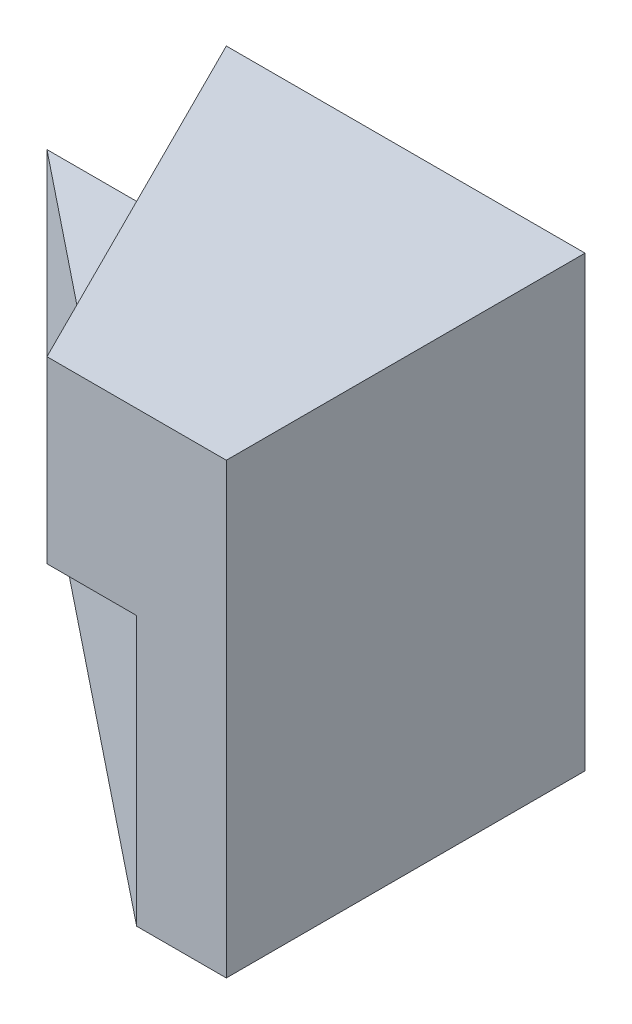
SolidWorks part; units mm, degrees
ref_plane "Front Plane" through (0, 0, 0) normal (0, 0, 1) x (1, 0, 0)
ref_plane "Top Plane" through (0, 0, 0) normal (0, 1, 0) x (1, 0, 0)
ref_plane "Right Plane" through (0, 0, 0) normal (1, 0, 0) x (0, 0, -1)
sketch "Sketch1" plane through (0, 0, 0) normal (0, 1, 0) x (1, 0, 0)
  line L0 (0, 0) -> (-5, 4)
  line L1 (-5, 4) -> (0, 4)
  line L2 (0, 4) -> (0, 0)
  dimension "D1" = 4
  dimension "D2" = 5
extrude "Boss-Extrude1" add sketch "Sketch1" along normal blind 3
sketch "Sketch2" plane through (0, 0, -4) normal (0, 0, -1) x (-1, 0, 0)
  line L0 (1, 5) -> (3, 5)
  line L1 (-1, 0) -> (-1, 5)
  line L2 (-1, 5) -> (1, 5)
  line L3 (-1, 0) -> (0, 0)
  line L4 (0, 3) -> (5, 3) construction
  line L5 (0, 0) -> (0, 3)
  line L6 (0, 3) -> (3, 3)
  line L7 (3, 5) -> (3, 3)
  dimension "D1" = 5
  dimension "D2" = 2
  dimension "D3" = 1
  dimension "D4" = 2
  dimension "D5" = 2
extrude "Boss-Extrude2" add sketch "Sketch2" against normal blind 4
sketch "Sketch4" plane through (0, 5, 0) normal (0, 1, 0) x (1, 0, 0)
  line L0 (-3, 4) -> (-1, 0)
  line L1 (-3, 0) -> (1, 0) construction
  line L2 (-1, 0) -> (-3, 0)
  line L3 (-3, 0) -> (-3, 4)
  dimension "D1" = 2
extrude "Cut-Extrude2" cut sketch "Sketch4" against normal blind 2
